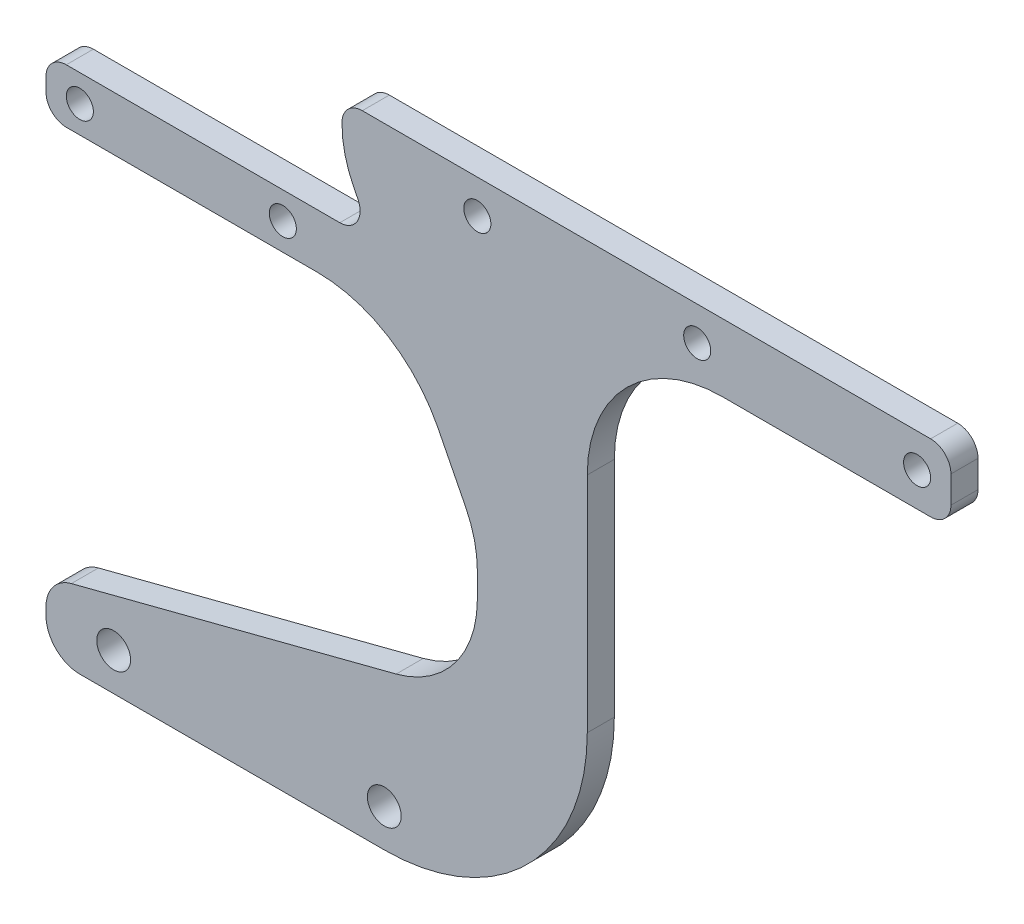
SolidWorks part; units mm, degrees
ref_plane "Front Plane" through (0, 0, 0) normal (0, 0, 1) x (1, 0, 0)
ref_plane "Top Plane" through (0, 0, 0) normal (0, 1, 0) x (1, 0, 0)
ref_plane "Right Plane" through (0, 0, 0) normal (1, 0, 0) x (0, 0, -1)
sketch "Sketch1" plane through (0, 0, 0) normal (0, 0, 1) x (1, 0, 0)
  line L20 (232.046, -14) -> (229.8248, -14) construction
  line L21 (271.9793, 5) -> (271.9793, -14) construction
  line L22 (325.7293, 5) -> (235.7293, 5) construction
  line L23 (249.8891, -24.9655) -> (254.0039, -33.0922)
  line L24 (194.9783, -6) -> (235.4063, -6)
  line L25 (191.9793, -11.001) -> (191.9793, -8.999)
  line L26 (232.046, -14) -> (194.9783, -14)
  line L27 (243.7384, -59.6035) -> (195.7265, -72.0301)
  line L28 (237.4548, -0.4078) -> (238.0819, -1.6463)
  line L29 (191.9793, -78) -> (191.9793, -76.8706)
  line L30 (241.9793, -83) -> (196.9793, -83)
  line L31 (255.7293, -40.3198) -> (255.7293, -44.1139)
  line L32 (271.9793, -53) -> (271.9793, -20)
  line L33 (288.2293, 5) -> (255.7293, 5)
  line L34 (325.7293, 5) -> (320.7293, 5)
  line L35 (235.7293, 7) -> (235.7293, 6.8198)
  line L36 (322.7293, 10) -> (238.7293, 10)
  line L37 (325.7293, 3) -> (325.7293, 7)
  line L38 (322.7293, 0) -> (291.9793, 0)
  circle A22 centre (226.9793, -10) radius 2.001
  circle A23 centre (196.9793, -10) radius 2.001
  arc A24 (249.8891, -24.9655) -> (232.046, -14) centre (232.046, -34) ccw
  arc A25 (194.9783, -14) -> (191.9793, -11.001) centre (194.9783, -11.001) cw
  arc A26 (191.9793, -8.999) -> (194.9783, -6) centre (194.9783, -8.999) cw
  arc A27 (235.4063, -6) -> (238.0819, -1.6463) centre (235.4063, -3.001) ccw
  arc A28 (235.7293, 6.8198) -> (237.4548, -0.4078) centre (251.7293, 6.8198) ccw
  circle A29 centre (201.9793, -77.4353) radius 2.5
  circle A30 centre (241.9793, -77.4353) radius 2.5
  arc A31 (255.7293, -44.1139) -> (243.7384, -59.6035) centre (239.7293, -44.1139) cw
  arc A32 (254.0039, -33.0922) -> (255.7293, -40.3198) centre (239.7293, -40.3198) cw
  arc A33 (191.9793, -76.8706) -> (195.7265, -72.0301) centre (196.9793, -76.8706) cw
  arc A34 (196.9793, -83) -> (191.9793, -78) centre (196.9793, -78) cw
  arc A35 (271.9793, -20) -> (291.9793, 0) centre (291.9793, -20) cw
  arc A36 (271.9793, -53) -> (241.9793, -83) centre (241.9793, -53) cw
  circle A37 centre (255.7293, 5) radius 2
  circle A38 centre (288.2293, 5) radius 2
  circle A39 centre (320.7293, 5) radius 2
  arc A40 (238.7293, 10) -> (235.7293, 7) centre (238.7293, 7) ccw
  arc A41 (322.7293, 10) -> (325.7293, 7) centre (322.7293, 7) cw
  arc A42 (322.7293, 0) -> (325.7293, 3) centre (322.7293, 3) ccw
  point P127 (226.9793, -10)
  point P128 (325.7293, 0)
extrude "Boss-Extrude2" add sketch "Sketch1" along normal blind 4
